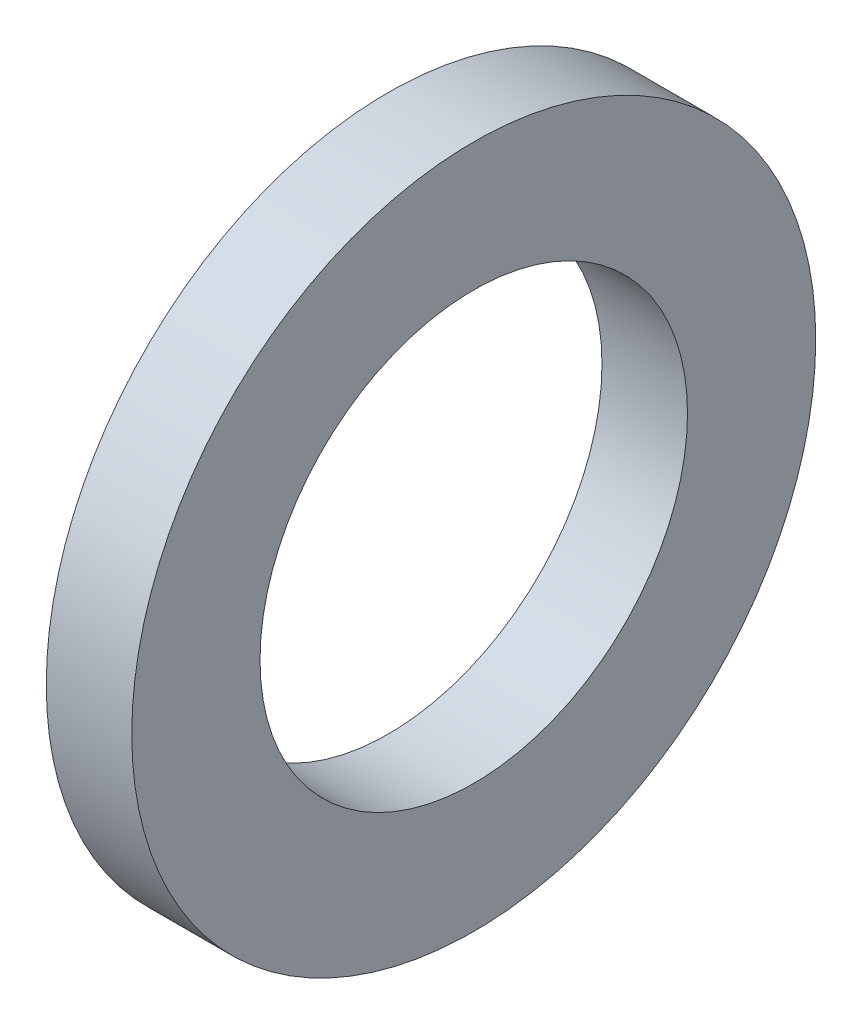
SolidWorks part; units mm, degrees
ref_plane "Спереди" through (0, 0, 0) normal (0, 0, 1) x (1, 0, 0)
ref_plane "Сверху" through (0, 0, 0) normal (0, 1, 0) x (1, 0, 0)
ref_plane "Справа" through (0, 0, 0) normal (1, 0, 0) x (0, 0, -1)
sketch "Эскиз2" plane through (0, 0, 0) normal (1, 0, 0) x (0, 0, -1)
  circle A0 centre (0, 0) radius 2.5
  circle A1 centre (0, 0) radius 4
  dimension "D1" = 5
  dimension "D2" = 8
extrude "Бобышка-Вытянуть1" add sketch "Эскиз2" along normal blind 1
